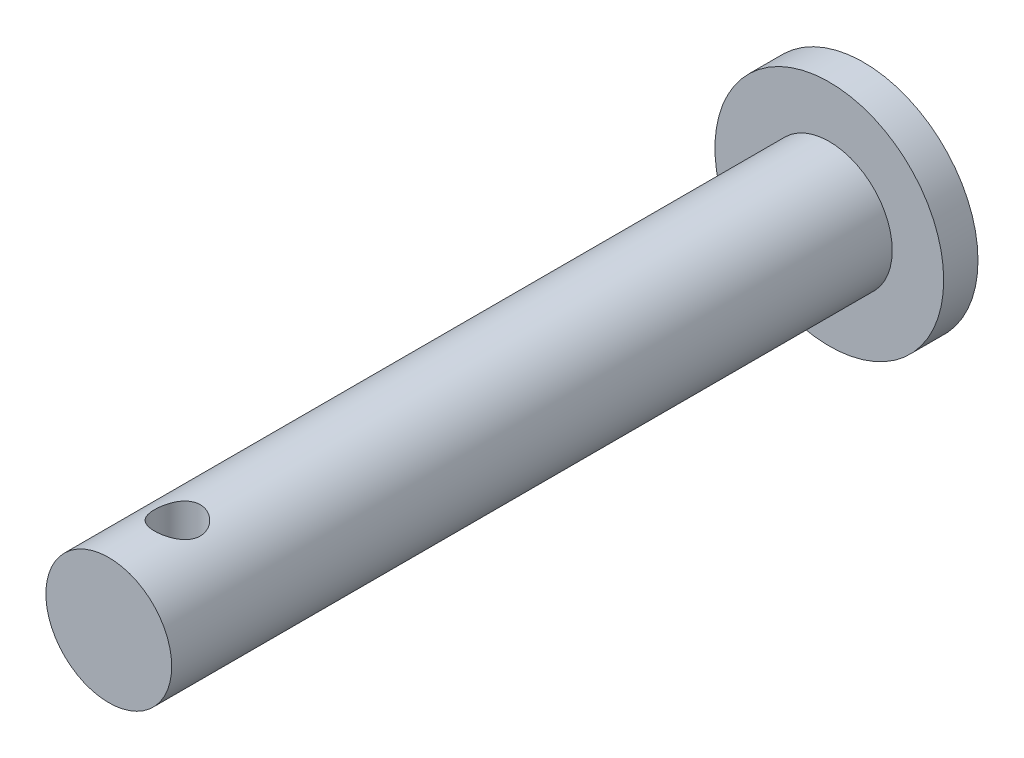
SolidWorks part; units mm, degrees
ref_plane "Front Plane" through (0, 0, 0) normal (0, 0, 1) x (1, 0, 0)
ref_plane "Top Plane" through (0, 0, 0) normal (0, 1, 0) x (1, 0, 0)
ref_plane "Right Plane" through (0, 0, 0) normal (1, 0, 0) x (0, 0, -1)
sketch "Sketch1" plane through (0, 0, 0) normal (0, 0, 1) x (1, 0, 0)
  circle A0 centre (0, 0) radius 5
  dimension "D1" = 10
extrude "Boss-Extrude1" add sketch "Sketch1" along normal blind 1.5
sketch "Sketch2" plane through (0, 0, 0) normal (0, 0, 1) x (1, 0, 0)
  circle A0 centre (0, 0) radius 2.75
  dimension "D1" = 5.5
extrude "Boss-Extrude2" add sketch "Sketch2" along normal blind 33
sketch "Sketch3" plane through (0, 0, 0) normal (0, 1, 0) x (1, 0, 0)
  line L0 (-2.75, -33) -> (2.75, -33) construction
  circle A0 centre (0, -30) radius 1
  dimension "D1" = 2
  dimension "D2" = 3
extrude "Cut-Extrude1" cut sketch "Sketch3" along normal through all
